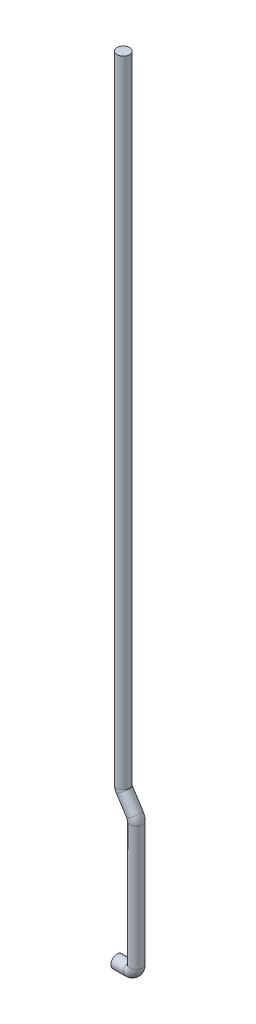
SolidWorks part; units mm, degrees
material "Copper"
ref_plane "Front Plane" through (0, 0, 0) normal (0, 0, 1) x (1, 0, 0)
ref_plane "Top Plane" through (0, 0, 0) normal (0, 1, 0) x (1, 0, 0)
ref_plane "Right Plane" through (0, 0, 0) normal (1, 0, 0) x (0, 0, -1)
sketch "Sketch3" plane through (0, 0, 0) normal (0, 0, 1) x (1, 0, 0)
  line L0 (0, 0) -> (8, 0)
  line L1 (12.3505, 4.3505) -> (12.3505, 84.0315)
  line L2 (11.3884, 87.3076) -> (4.6877, 97.731)
  line L8 (3.9968, 508.1288) -> (3.9968, 100.0836)
  arc A1 (8, 0) -> (12.3505, 4.3505) centre (8, 4.3505) ccw
  arc A3 (12.3505, 84.0315) -> (11.3884, 87.3076) centre (6.2921, 84.0315) ccw
  arc A4 (4.6877, 97.731) -> (3.9968, 100.0836) centre (8.3473, 100.0836) cw
  point P6 (0, 0)
  point P7 (0, 0)
  point P8 (0, 0)
  point P15 (2, 8)
  point P18 (12.3505, 0)
  point P21 (2, 85.8109)
  point P24 (12.3505, 85.8109)
  dimension "D1" = 4.3505
  dimension "D2" = 8
sketch "Sketch17" plane through (0, 0, 0) normal (1, 0, 0) x (0, 0, -1)
  circle A0 centre (0, 0) radius 4
sweep "Sweep22" add profiles "Sketch17" path "Sketch3"
